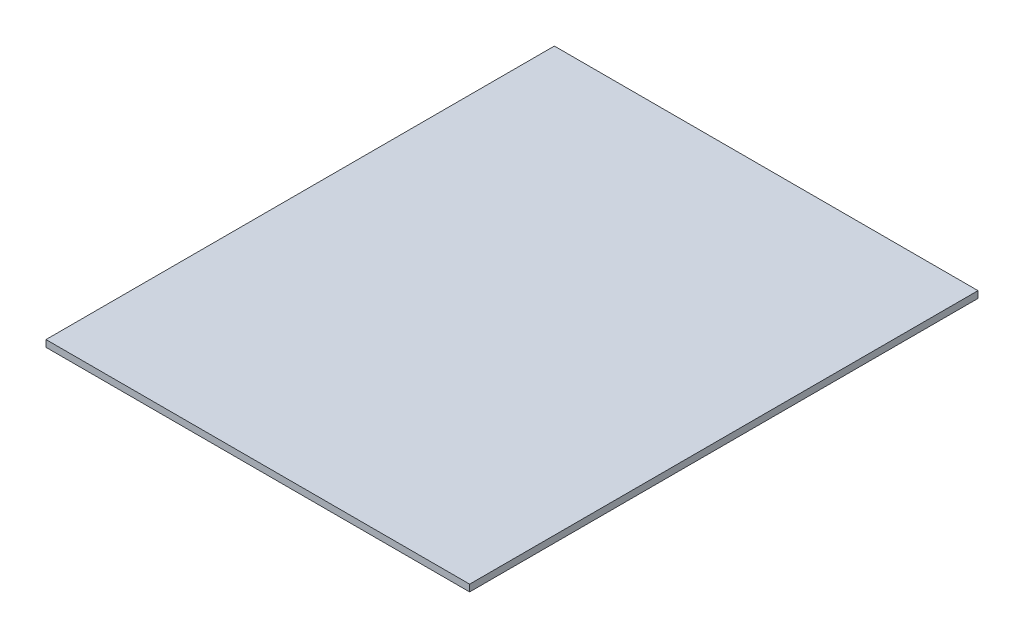
SolidWorks part; units mm, degrees
material "1023 Carbon Steel Sheet (SS)"
ref_plane "Front Plane" through (0, 0, 0) normal (0, 0, 1) x (1, 0, 0)
ref_plane "Top Plane" through (0, 0, 0) normal (0, 1, 0) x (1, 0, 0)
ref_plane "Right Plane" through (0, 0, 0) normal (1, 0, 0) x (0, 0, -1)
sketch "Sketch1" plane through (0, 0, 0) normal (0, 1, 0) x (1, 0, 0)
  line L1 (-158.75, -190.5) -> (158.75, -190.5)
  line L2 (-158.75, -190.5) -> (-158.75, 190.5)
  line L3 (-158.75, 190.5) -> (158.75, 190.5)
  line L4 (158.75, -190.5) -> (158.75, 190.5)
  line L5 (-158.75, -190.5) -> (158.75, 190.5) construction
  line L6 (-158.75, 190.5) -> (158.75, -190.5) construction
  point P0 (0, 0)
  dimension "D1" = 381
  dimension "D2" = 317.5
extrude "Boss-Extrude1" add sketch "Sketch1" along normal blind 5.08
